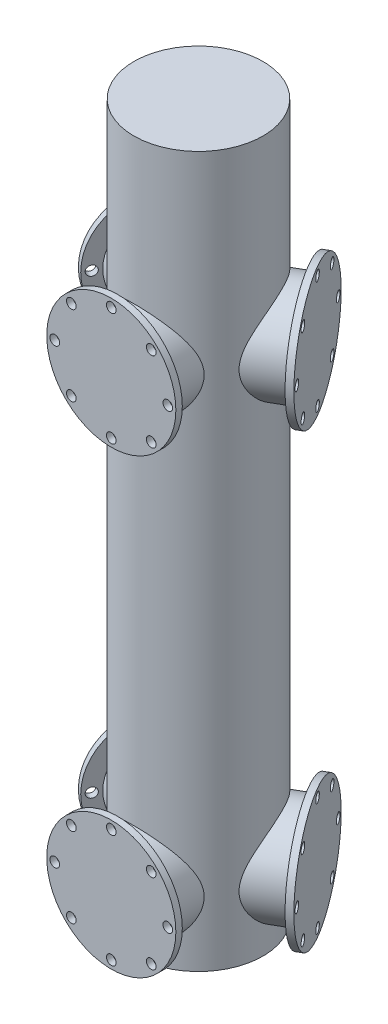
SolidWorks part; units mm, degrees
material "Plain Carbon Steel"
ref_plane "Front Plane" through (0, 0, 0) normal (0, 0, 1) x (1, 0, 0)
ref_plane "Top Plane" through (0, 0, 0) normal (0, 1, 0) x (1, 0, 0)
ref_plane "Right Plane" through (0, 0, 0) normal (1, 0, 0) x (0, 0, -1)
sketch "Sketch1" plane through (0, 0, 0) normal (0, 1, 0) x (1, 0, 0)
  circle A0 centre (0, 0) radius 20
  dimension "D1" = 40
extrude "Boss-Extrude1" add sketch "Sketch1" along normal blind 220
sketch "Sketch2" plane through (0, 0, 0) normal (0, 0, 1) x (1, 0, 0)
  circle A0 centre (0, 160) radius 15
  circle A1 centre (0, 20) radius 15
  point P4 (25.1276, 168.1327)
  dimension "D1" = 30
  dimension "D2" = 30
  dimension "D6" = 160
  dimension "D3" = 160
  dimension "D4" = 20
  dimension "D5" = 140
extrude "Boss-Extrude2" add sketch "Sketch2" along normal blind 25
sketch "Sketch3" plane through (0, 0, 25) normal (0, 0, 1) x (1, 0, 0)
  circle A0 centre (0, 160) radius 20
  circle A2 centre (0, 177.5) radius 1.5
  circle A3 centre (12.3744, 172.3744) radius 1.5
  circle A4 centre (17.5, 160) radius 1.5
  circle A5 centre (12.3744, 147.6256) radius 1.5
  circle A6 centre (0, 142.5) radius 1.5
  circle A7 centre (-12.3744, 147.6256) radius 1.5
  circle A8 centre (-17.5, 160) radius 1.5
  circle A9 centre (-12.3744, 172.3744) radius 1.5
  circle A10 centre (0, 20) radius 20
  circle A11 centre (0, 37.5) radius 1.5
  circle A12 centre (12.3744, 32.3744) radius 1.5
  circle A13 centre (17.5, 20) radius 1.5
  circle A14 centre (12.3744, 7.6256) radius 1.5
  circle A15 centre (0, 2.5) radius 1.5
  circle A16 centre (-12.3744, 7.6256) radius 1.5
  circle A17 centre (-17.5, 20) radius 1.5
  circle A18 centre (-12.3744, 32.3744) radius 1.5
  point P24 (0, 160)
  point P43 (0, 20)
  dimension "D1" = 40
  dimension "D2" = 17.5
  dimension "D3" = 3
  dimension "D4" = 17.5
  dimension "D5" = 17.5
  dimension "D7" = 0
  dimension "D6" = 2
extrude "Boss-Extrude4" add sketch "Sketch3" along normal blind 2
pattern_circular "CirPattern1" count 3 over 360 about axis through (0, 0, 0) along (0, 1, 0) of "Boss-Extrude2", "Boss-Extrude4"
